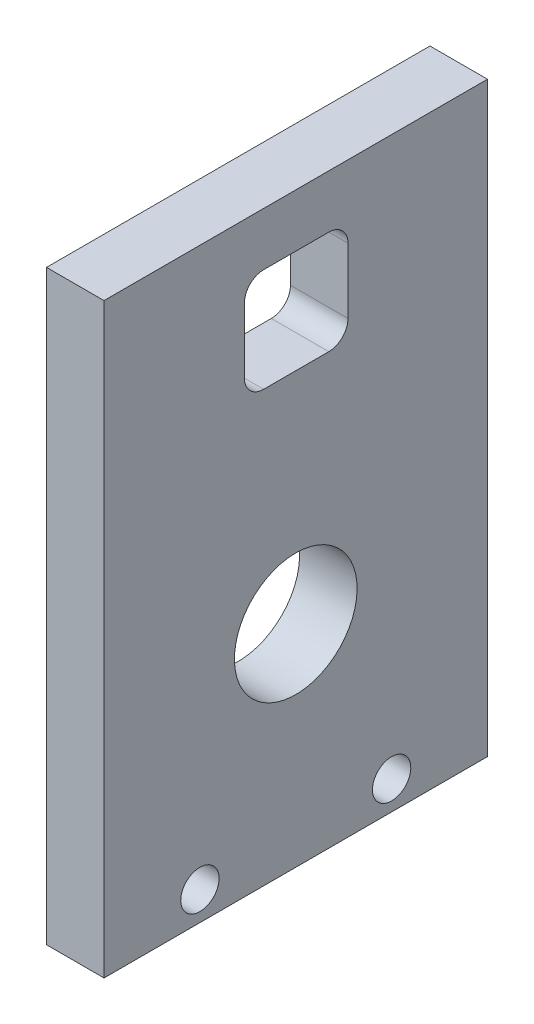
SolidWorks part; units mm, degrees
ref_plane "Ön Düzlem" through (0, 0, 0) normal (0, 0, 1) x (1, 0, 0)
ref_plane "Üst Düzlem" through (0, 0, 0) normal (0, 1, 0) x (1, 0, 0)
ref_plane "Sağ Düzlem" through (0, 0, 0) normal (1, 0, 0) x (0, 0, -1)
sketch "Çizim1" plane through (0, 0, 0) normal (0, 0, 1) x (1, 0, 0)
  line L1 (-7.5, 76.5) -> (7.5, 76.5)
  line L2 (-7.5, 76.5) -> (-7.5, -76.5)
  line L3 (-7.5, -76.5) -> (7.5, -76.5)
  line L4 (7.5, 76.5) -> (7.5, -76.5)
  line L5 (-7.5, 76.5) -> (7.5, -76.5) construction
  line L6 (-7.5, -76.5) -> (7.5, 76.5) construction
  point P0 (0, 0)
extrude "Yükseklik-Ekstrüzyon1" add sketch "Çizim1" along normal blind 100
ref_plane "Düzlem1" through (7.5, 0, 0) normal (1, 0, 0) x (0, 0, -1)
sketch "Çizim2" plane through (7.5, 0, 0) normal (1, 0, 0) x (0, 0, -1)
  circle A0 centre (-75, -69) radius 5
  circle A1 centre (-25, -69) radius 5
sketch "Çizim3" plane through (7.5, 0, 0) normal (1, 0, 0) x (0, 0, -1)
  line L1 (-58.3841, 35.6537) -> (-41.3841, 35.6537)
  line L2 (-63.3841, 40.6537) -> (-63.3841, 57.6537)
  line L3 (-58.3841, 62.6537) -> (-41.3841, 62.6537)
  line L4 (-36.3841, 40.6537) -> (-36.3841, 57.6537)
  line L5 (-63.3841, 35.6537) -> (-36.3841, 62.6537) construction
  line L6 (-63.3841, 62.6537) -> (-36.3841, 35.6537) construction
  circle A0 centre (-50, -21.5) radius 16
  arc A2 (-41.3841, 35.6537) -> (-36.3841, 40.6537) centre (-41.3841, 40.6537) ccw
  arc A3 (-58.3841, 35.6537) -> (-63.3841, 40.6537) centre (-58.3841, 40.6537) cw
  arc A4 (-41.3841, 62.6537) -> (-36.3841, 57.6537) centre (-41.3841, 57.6537) cw
  arc A5 (-63.3841, 57.6537) -> (-58.3841, 62.6537) centre (-58.3841, 57.6537) cw
  dimension "D1" = 5
extrude "Kes-Ekstrüzyon2" cut sketch "Çizim2" against normal through all
extrude "Kes-Ekstrüzyon3" cut sketch "Çizim3" against normal through all
